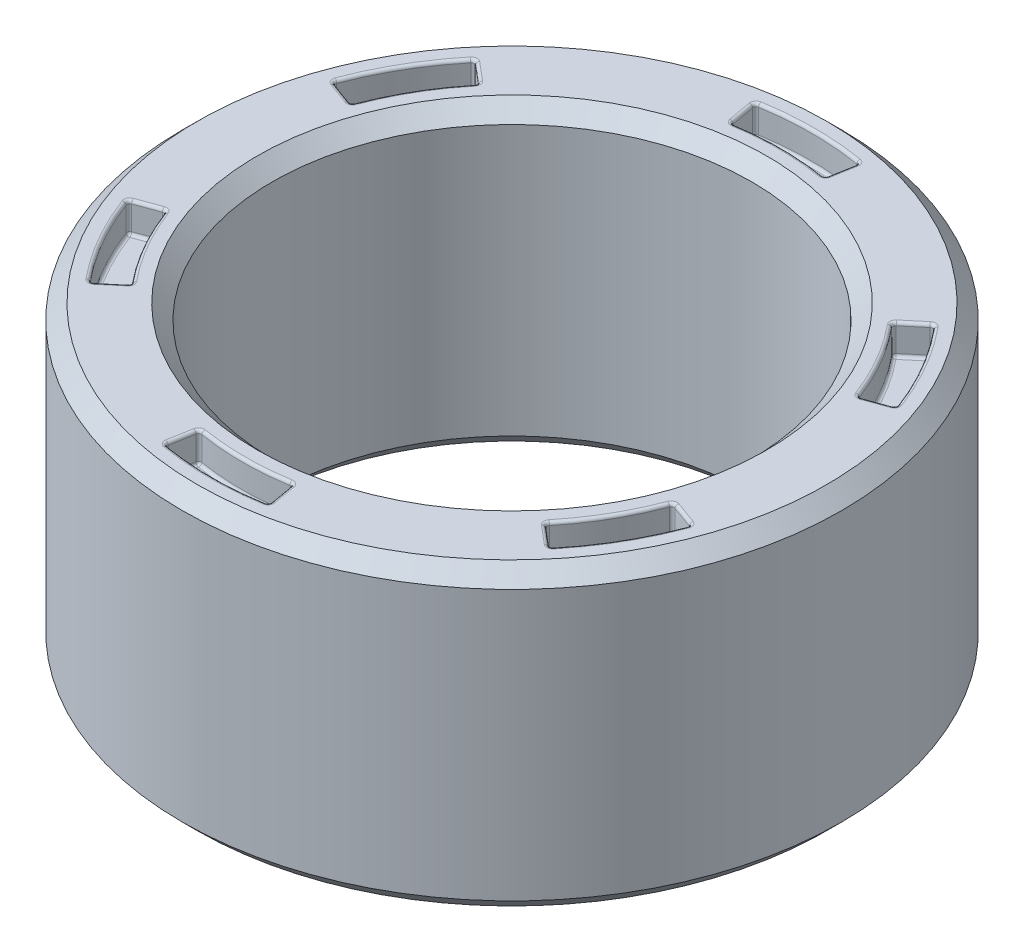
SolidWorks part; units mm, degrees
ref_plane "Front Plane" through (0, 0, 0) normal (0, 0, 1) x (1, 0, 0)
ref_plane "Top Plane" through (0, 0, 0) normal (0, 1, 0) x (1, 0, 0)
ref_plane "Right Plane" through (0, 0, 0) normal (1, 0, 0) x (0, 0, -1)
sketch "Sketch1" plane through (0, 0, 0) normal (0, 1, 0) x (1, 0, 0)
  circle A0 centre (0, 0) radius 11
  circle A1 centre (0, 0) radius 8
  dimension "D1" = 22
  dimension "D2" = 16
extrude "Boss-Extrude1" add sketch "Sketch1" along normal blind 10
chamfer "Chamfer1" distance 0.5 angle 45 4 edges at (0, 0, 8) (0, 0, 11) (0, 10, 11) (0, 10, 8)
sketch "Sketch2" plane through (0, 10, 0) normal (0, 1, 0) x (1, 0, 0)
  line L0 (0, 0) -> (0, 9) construction
  line L1 (0, 0) -> (1.5628, 8.8633) construction
  line L2 (0, 0) -> (-1.5628, 8.8633) construction
  line L3 (-1.5628, 8.8633) -> (-1.7365, 9.8481)
  line L4 (1.5628, 8.8633) -> (1.7365, 9.8481)
  circle A0 centre (0, 0) radius 9 construction
  circle A1 centre (0, 0) radius 10 construction
  arc A2 (1.5628, 8.8633) -> (-1.5628, 8.8633) centre (0, 0) ccw
  arc A3 (1.7365, 9.8481) -> (-1.7365, 9.8481) centre (0, 0) ccw
  dimension "D1" = 18
  dimension "D2" = 20
  dimension "D3" = 10
extrude "Cut-Extrude1" cut sketch "Sketch2" against normal blind 1
fillet "Fillet1" radius 0.1 12 edges at (1.5628, 9.5, -8.8633) (1.7365, 9.5, -9.8481) (1.6497, 10, -9.3557) (1.6497, 9, -9.3557) (-1.7365, 9.5, -9.8481) (-1.5628, 9.5, -8.8633) (-1.6497, 10, -9.3557) (-1.6497, 9, -9.3557) (0, 10, -9) (0, 9, -9) (0, 10, -10) (0, 9, -10)
pattern_circular "CirPattern1" count 6 over 360 about axis through (0, 0, 0) along (0, 1, 0) of "Cut-Extrude1", "Fillet1"
